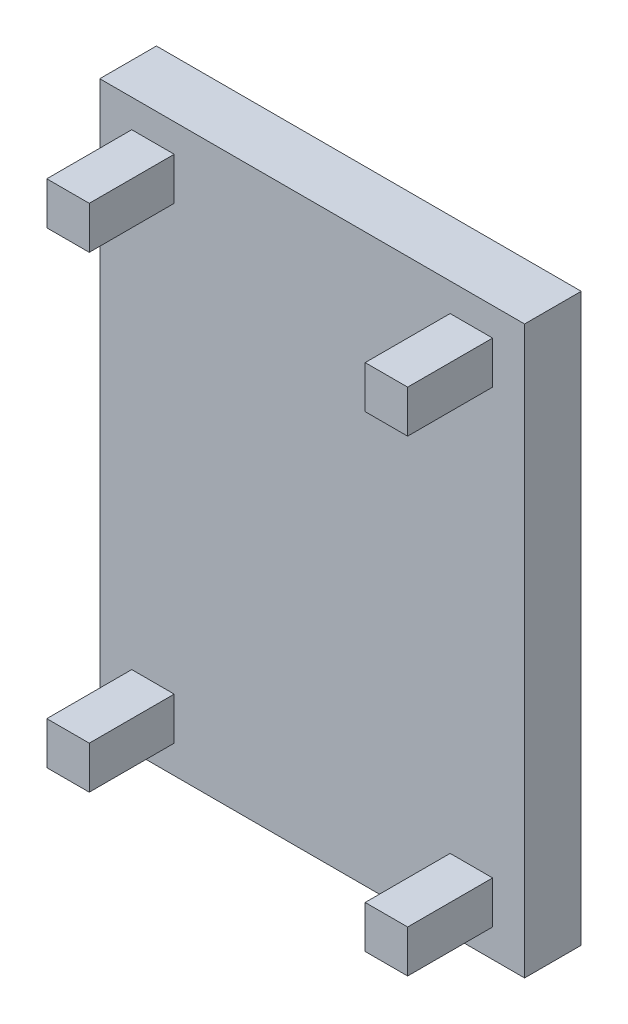
SolidWorks part; units mm, degrees
ref_plane "前视基准面" through (0, 0, 0) normal (0, 0, 1) x (1, 0, 0)
ref_plane "上视基准面" through (0, 0, 0) normal (0, 1, 0) x (1, 0, 0)
ref_plane "右视基准面" through (0, 0, 0) normal (1, 0, 0) x (0, 0, -1)
sketch "草图1" plane through (0, 0, 0) normal (0, 0, 1) x (1, 0, 0)
  line L1 (-750, -1000) -> (750, -1000)
  line L2 (-750, -1000) -> (-750, 1000)
  line L3 (-750, 1000) -> (750, 1000)
  line L4 (750, -1000) -> (750, 1000)
  line L5 (-750, -1000) -> (750, 1000) construction
  line L6 (-750, 1000) -> (750, -1000) construction
  point P0 (0, 0)
  dimension "D1" = 2000
  dimension "D2" = 1500
extrude "凸台-拉伸1" add sketch "草图1" along normal blind 200
sketch "草图2" plane through (0, 0, 200) normal (0, 0, 1) x (1, 0, 0)
  line L1 (-637.1011, 750.4231) -> (-487.1011, 750.4231)
  line L2 (-637.1011, 750.4231) -> (-637.1011, 900.4231)
  line L3 (-637.1011, 900.4231) -> (-487.1011, 900.4231)
  line L4 (-487.1011, 750.4231) -> (-487.1011, 900.4231)
  line L5 (-637.1011, 750.4231) -> (-487.1011, 900.4231) construction
  line L6 (-637.1011, 900.4231) -> (-487.1011, 750.4231) construction
  line L8 (637.1011, 900.4231) -> (487.1011, 750.4231) construction
  line L9 (637.1011, 750.4231) -> (487.1011, 900.4231) construction
  line L10 (487.1011, 750.4231) -> (487.1011, 900.4231)
  line L11 (637.1011, 900.4231) -> (487.1011, 900.4231)
  line L12 (637.1011, 750.4231) -> (637.1011, 900.4231)
  line L13 (637.1011, 750.4231) -> (487.1011, 750.4231)
  line L14 (637.1011, -750.4231) -> (487.1011, -900.4231) construction
  line L15 (637.1011, -900.4231) -> (487.1011, -750.4231) construction
  line L16 (-637.1011, -900.4231) -> (-487.1011, -750.4231) construction
  line L17 (-637.1011, -750.4231) -> (-487.1011, -900.4231) construction
  line L18 (637.1011, -750.4231) -> (487.1011, -750.4231)
  line L19 (637.1011, -750.4231) -> (637.1011, -900.4231)
  line L20 (637.1011, -900.4231) -> (487.1011, -900.4231)
  line L21 (487.1011, -750.4231) -> (487.1011, -900.4231)
  line L22 (-487.1011, -750.4231) -> (-487.1011, -900.4231)
  line L23 (-637.1011, -900.4231) -> (-487.1011, -900.4231)
  line L24 (-637.1011, -750.4231) -> (-637.1011, -900.4231)
  line L25 (-637.1011, -750.4231) -> (-487.1011, -750.4231)
  point P0 (-562.1011, 825.4231)
  point P13 (562.1011, 825.4231)
  point P22 (562.1011, -825.4231)
  point P23 (-562.1011, -825.4231)
  dimension "D1" = 150
  dimension "D2" = 150
extrude "凸台-拉伸2" add sketch "草图2" along normal blind 300
